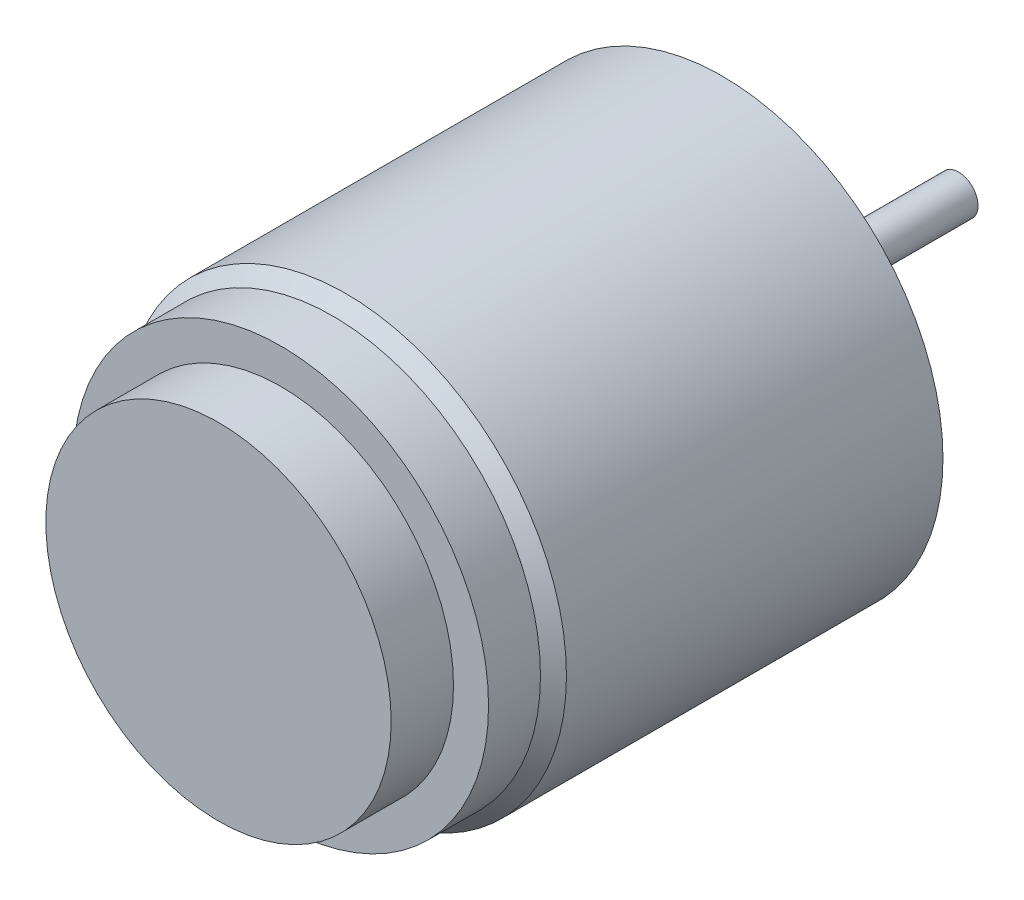
SolidWorks part; units mm, degrees
ref_plane "Front Plane" through (0, 0, 0) normal (0, 0, 1) x (1, 0, 0)
ref_plane "Top Plane" through (0, 0, 0) normal (0, 1, 0) x (1, 0, 0)
ref_plane "Right Plane" through (0, 0, 0) normal (1, 0, 0) x (0, 0, -1)
sketch "Sketch2" plane through (0, 0, 0) normal (0, 0, 1) x (1, 0, 0)
  circle A0 centre (0, 0) radius 8.5
  dimension "D1" = 17
extrude "Boss-Extrude1" add sketch "Sketch2" along normal blind 15
chamfer "Chamfer1" distance 0.5 angle 45 1 edges at (8.5, 0, 15)
sketch "Sketch3" plane through (0, 0, 15) normal (0, 0, 1) x (1, 0, 0)
  circle A0 centre (0, 0) radius 8
  dimension "D1" = 16
extrude "Boss-Extrude2" add sketch "Sketch3" along normal blind 2
sketch "Sketch4" plane through (0, 0, 17) normal (0, 0, 1) x (1, 0, 0)
  circle A0 centre (0, 0) radius 6.65
  dimension "D1" = 13.3
extrude "Boss-Extrude3" add sketch "Sketch4" along normal blind 2.4
sketch "Sketch5" plane through (0, 0, 0) normal (0, 0, -1) x (-1, 0, 0)
  line L0 (0, 0) -> (0, 6.481) construction
  circle A0 centre (0, 0) radius 5
  circle A1 centre (0, 5) radius 0.8
  circle A2 centre (4.3301, 2.5) radius 0.8
  circle A3 centre (4.3301, -2.5) radius 0.8
  circle A4 centre (0, -5) radius 0.8
  circle A5 centre (-4.3301, -2.5) radius 0.8
  circle A6 centre (-4.3301, 2.5) radius 0.8
  point P19 (0, 0)
  dimension "D1" = 10
  dimension "D2" = 1.6
  dimension "D3" = 6
extrude "Cut-Extrude1" cut sketch "Sketch5" against normal blind 1.6 contours A6 | A1 | A2 | A3 | A4 | A5
sketch "Sketch6" plane through (0, 0, 0) normal (0, 0, -1) x (-1, 0, 0)
  circle A0 centre (0, 0) radius 3
  dimension "D1" = 6
extrude "Boss-Extrude4" add sketch "Sketch6" along normal blind 1
sketch "Sketch7" plane through (0, 0, -1) normal (0, 0, -1) x (-1, 0, 0)
  circle A0 centre (0, 0) radius 1.75
  dimension "D1" = 3.5
extrude "Boss-Extrude5" add sketch "Sketch7" along normal blind 2.1 contours A0
sketch "Sketch8" plane through (0, 0, -3.1) normal (0, 0, -1) x (-1, 0, 0)
  circle A0 centre (0, 0) radius 0.75
  dimension "D1" = 1.5
extrude "Boss-Extrude6" add sketch "Sketch8" along normal blind 6
